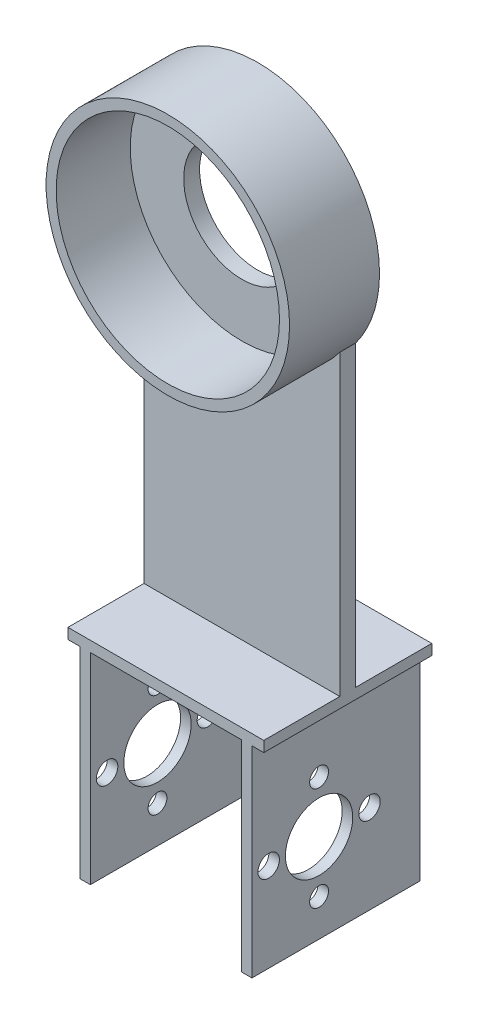
SolidWorks part; units mm, degrees
ref_plane "Front Plane" through (0, 0, 0) normal (0, 0, 1) x (1, 0, 0)
ref_plane "Top Plane" through (0, 0, 0) normal (0, 1, 0) x (1, 0, 0)
ref_plane "Right Plane" through (0, 0, 0) normal (1, 0, 0) x (0, 0, -1)
sketch "Sketch1" plane through (0, 0, 0) normal (0, 1, 0) x (1, 0, 0)
  line L0 (-3.0743, 1.2077) -> (-1.0743, 1.2077)
  line L1 (-3.0743, 1.2077) -> (-3.0743, -30.5323)
  line L2 (-1.0743, 1.2077) -> (-1.0743, -30.5323)
  line L3 (-3.0743, -30.5323) -> (-1.0743, -30.5323)
  line L4 (13.1897, 10.0004) -> (13.1897, -34.5364) construction
  line L5 (27.4537, 1.2077) -> (27.4537, -30.5323)
  line L6 (29.4537, -30.5323) -> (27.4537, -30.5323)
  line L7 (29.4537, 1.2077) -> (29.4537, -30.5323)
  line L8 (29.4537, 1.2077) -> (27.4537, 1.2077)
  dimension "D1" = 2
  dimension "D2" = 31.74
  dimension "D3" = 16.264
extrude "Boss-Extrude1" add sketch "Sketch1" along normal blind 40
ref_plane "Plane1" through (0, 40, 0) normal (0, 1, 0) x (1, 0, 0)
sketch "Sketch2" plane through (0, 40, 0) normal (0, 1, 0) x (1, 0, 0)
  line L0 (-5.3063, 1.2077) -> (31.6937, 1.2077)
  line L1 (-5.3063, 1.2077) -> (-5.3063, -30.5323)
  line L2 (31.6937, 1.2077) -> (31.6937, -30.5323)
  line L3 (-5.3063, -30.5323) -> (31.6937, -30.5323)
  line L4 (27.4537, -30.5323) -> (29.4537, -30.5323) construction
  line L5 (29.4537, 1.2077) -> (27.4537, 1.2077) construction
  line L6 (13.1937, -30.5323) -> (13.1937, 15.7517) construction
  line L7 (13.1937, 15.7517) -> (13.1937, -60.8234) construction
  line L8 (27.4537, 1.2077) -> (27.4537, -30.5323) construction
  line L9 (-1.0743, -30.5323) -> (-1.0743, 1.2077) construction
  dimension "D1" = 37
  dimension "D2" = 14.26
  dimension "D3" = 14.268
  dimension "D4" = 18.5
  dimension "D5" = 18.5
extrude "Boss-Extrude3" add sketch "Sketch2" against normal blind 2
sketch "Sketch8" plane through (0, 40, 0) normal (0, 1, 0) x (1, 0, 0)
  line L0 (-5.3063, -13.1623) -> (-5.3063, -16.1623)
  line L1 (-5.3063, -13.1623) -> (31.6937, -13.1623)
  line L2 (-5.3063, -16.1623) -> (31.6937, -16.1623)
  line L3 (31.6937, -13.1623) -> (31.6937, -16.1623)
  line L4 (-5.3063, 1.2077) -> (-5.3063, -30.5323) construction
  line L6 (31.6937, -30.5323) -> (31.6937, 1.2077) construction
  point P6 (-5.3063, -14.6623)
  dimension "D1" = 3
  dimension "D2" = 1.5
  dimension "D3" = 15.87
  dimension "D4" = 15.87
extrude "Boss-Extrude4" add sketch "Sketch8" along normal blind 70
sketch "Sketch20" plane through (29.4537, 0, 0) normal (1, 0, 0) x (0, 0, -1)
  line L0 (-1026.1464, 0.0159) -> (48973.8536, 0.0159) construction
  line L2 (-1020.6004, 7.0009) -> (48979.3996, 7.0009)
  line L3 (1.2077, -967.9144) -> (1.2077, 49032.0856) construction
  line L4 (-1022.4653, 16.7799) -> (48977.5347, 16.7799)
  line L6 (-1017.7509, 26.5589) -> (48982.2491, 26.5589)
  line L7 (-8.3173, -967.0415) -> (-8.3173, 49032.9585)
  line L8 (-17.8423, -967.8053) -> (-17.8423, 49032.1947)
  line L10 (-27.3673, -967.9144) -> (-27.3673, 49032.0856)
  circle A0 centre (-17.8423, 16.7799) radius 6.36
  circle A1 centre (-17.8423, 26.5589) radius 1.78
  circle A2 centre (-17.8423, 7.0009) radius 1.78
  circle A3 centre (-27.3673, 16.7799) radius 2.03
  circle A4 centre (-8.3173, 16.7799) radius 2.03
  dimension "D7" = 9.779
  dimension "D1" = 6.985
  dimension "D2" = 26.543
  dimension "D3" = 16.764
  dimension "D4" = 9.525
  dimension "D5" = 19.05
  dimension "D6" = 28.575
  dimension "D8" = 9.779
  dimension "D9" = 9.525
  dimension "D10" = 9.525
sketch "Sketch22" plane through (29.4537, 0, 0) normal (1, 0, 0) x (0, 0, -1)
extrude "Cut-Extrude4" cut sketch "Sketch20" against normal through all both and the other way through all
sketch "Sketch23" plane through (0, 0, 16.1623) normal (0, 0, 1) x (1, 0, 0)
  line L0 (-5.3063, 110) -> (31.6937, 110) construction
  circle A0 centre (13.1937, 110) radius 23
extrude "Boss-Extrude6" add sketch "Sketch23" along normal blind 14 and the other way blind 3
sketch "Sketch24" plane through (0, 0, 16.1623) normal (0, 0, 1) x (1, 0, 0)
  line L0 (13.1937, -867) -> (13.1937, 49133) construction
  line L1 (-986.8063, 110) -> (49013.1937, 110) construction
  arc A0 (31.6937, 96.3343) -> (-5.3063, 96.3343) centre (13.1937, 110) ccw construction
  point P6 (13.1937, 133)
sketch "Sketch25" plane through (0, 0, 30.1623) normal (0, 0, 1) x (1, 0, 0)
  line L0 (13.1937, -200867) -> (13.1937, 249133) construction
  line L1 (-200986.8063, 110) -> (249013.1937, 110) construction
  circle A0 centre (13.1937, 110) radius 21.1
extrude "Cut-Extrude5" cut sketch "Sketch25" against normal blind 14
sketch "Sketch26" plane through (0, 0, 16.1623) normal (0, 0, 1) x (1, 0, 0)
  line L0 (13.1937, -200867) -> (13.1937, 249133) construction
  line L1 (-200986.8063, 110) -> (249013.1937, 110) construction
  circle A0 centre (13.1937, 110) radius 11
extrude "Cut-Extrude6" cut sketch "Sketch26" along normal through all both and the other way through all
